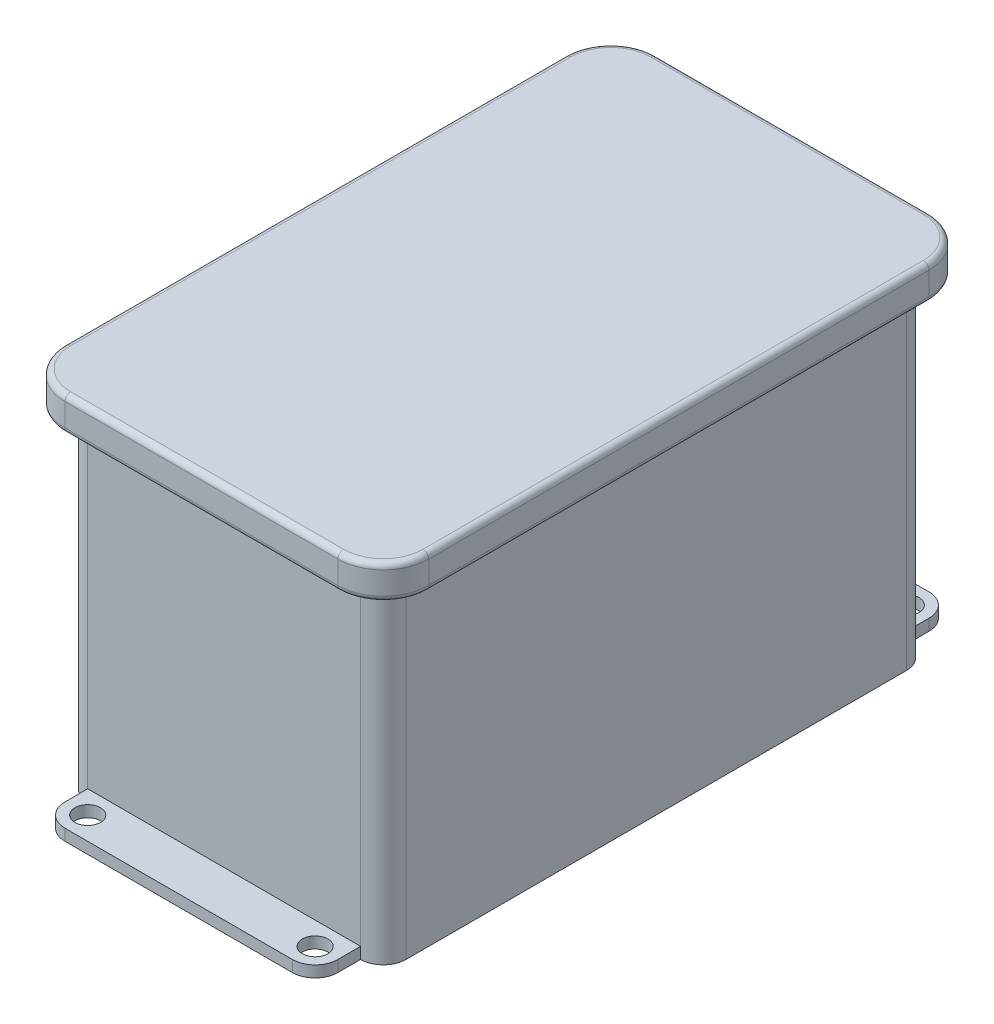
SolidWorks part; units mm, degrees
ref_plane "Front" through (0, 0, 0) normal (0, 0, 1) x (1, 0, 0)
ref_plane "Top" through (0, 0, 0) normal (0, 1, 0) x (1, 0, 0)
ref_plane "Right" through (0, 0, 0) normal (1, 0, 0) x (0, 0, -1)
sketch "Sketch1" plane through (0, 0, 0) normal (0, 1, 0) x (1, 0, 0)
  line L1 (0, 0) -> (88.9, 0)
  line L2 (0, 0) -> (0, 152.4)
  line L3 (0, 152.4) -> (88.9, 152.4)
  line L4 (88.9, 0) -> (88.9, 152.4)
  dimension "D1" = 152.4
  dimension "D2" = 88.9
extrude "Boss-Extrude1" add sketch "Sketch1" along normal blind 101.6
sketch "Sketch2" plane through (0, 0, 0) normal (0, -1, 0) x (1, 0, 0)
  line L0 (44.45, -152.4) -> (44.45, -158.75) construction
  line L1 (76.2, -158.75) -> (12.7, -158.75) construction
  line L2 (76.2, -165.1) -> (12.7, -165.1)
  line L4 (0, 0) -> (0, -152.4)
  line L5 (0, -152.4) -> (88.9, -152.4)
  line L6 (88.9, -152.4) -> (88.9, 0)
  line L7 (88.9, 0) -> (0, 0)
  line L9 (0, -152.4) -> (88.9, -152.4)
  line L12 (6.35, -158.75) -> (6.35, -152.4)
  line L14 (82.55, -158.75) -> (82.55, -152.4)
  arc A0 (76.2, -165.1) -> (82.55, -158.75) centre (76.2, -158.75) ccw
  arc A1 (6.35, -158.75) -> (12.7, -165.1) centre (12.7, -158.75) ccw
  circle A2 centre (12.7, -158.75) radius 3.5719
  circle A3 centre (76.2, -158.75) radius 3.5719
  point P8 (44.45, -158.75)
  point P12 (44.45, -158.75)
  dimension "D3" = 7.1437
  dimension "D2" = 76.2
  dimension "D4" = 12.7
  dimension "D5" = 6.35
  dimension "D1" = 0
extrude "Boss-Extrude2" add sketch "Sketch2" against normal blind 3.175 separate body contours L12 A1 L2 A0 L14 L9 A3 A2
ref_plane "Plane1" through (0, 0, -76.2) normal (0, 0, -1) x (-1, 0, 0)
mirror "Mirror2" about plane through (0, 0, -76.2) normal (0, 0, -1) of bodies 102
fillet "Fillet1" radius 6.35 4 edges at (88.9, 50.8, -152.4) (88.9, 50.8, 0) (0, 50.8, 0) (0, 50.8, -152.4)
sketch "Sketch4" plane through (0, 101.6, 0) normal (0, 1, 0) x (1, 0, 0)
  line L0 (95.25, 6.35) -> (95.25, 146.05)
  line L1 (82.55, 158.75) -> (6.35, 158.75)
  line L2 (-6.35, 146.05) -> (-6.35, 6.35)
  line L3 (6.35, -6.35) -> (82.55, -6.35)
  line L4 (88.9, 6.35) -> (88.9, 146.05)
  line L5 (82.55, 152.4) -> (6.35, 152.4)
  line L6 (0, 146.05) -> (0, 6.35)
  line L7 (6.35, 0) -> (82.55, 0)
  line L8 (88.9, 6.35) -> (88.9, 146.05) construction
  line L9 (82.55, 152.4) -> (6.35, 152.4) construction
  line L10 (0, 146.05) -> (0, 6.35) construction
  line L11 (6.35, 0) -> (82.55, 0) construction
  arc A0 (95.25, 146.05) -> (82.55, 158.75) centre (82.55, 146.05) ccw
  arc A1 (6.35, 158.75) -> (-6.35, 146.05) centre (6.35, 146.05) ccw
  arc A2 (-6.35, 6.35) -> (6.35, -6.35) centre (6.35, 6.35) ccw
  arc A3 (82.55, -6.35) -> (95.25, 6.35) centre (82.55, 6.35) ccw
  arc A4 (88.9, 146.05) -> (82.55, 152.4) centre (82.55, 146.05) ccw
  arc A5 (6.35, 152.4) -> (0, 146.05) centre (6.35, 146.05) ccw
  arc A6 (0, 6.35) -> (6.35, 0) centre (6.35, 6.35) ccw
  arc A7 (82.55, 0) -> (88.9, 6.35) centre (82.55, 6.35) ccw
  arc A8 (88.9, 146.05) -> (82.55, 152.4) centre (82.55, 146.05) ccw construction
  arc A9 (6.35, 152.4) -> (0, 146.05) centre (6.35, 146.05) ccw construction
  arc A10 (0, 6.35) -> (6.35, 0) centre (6.35, 6.35) ccw construction
  arc A11 (82.55, 0) -> (88.9, 6.35) centre (82.55, 6.35) ccw construction
  dimension "D1" = 0
  dimension "D2" = 6.35
extrude "Boss-Extrude3" add sketch "Sketch4" against normal blind 9.525
fillet "Fillet2" radius 1.5875 16 edges at (-2.6303, 92.075, -155.0303) (44.45, 92.075, -158.75) (91.5303, 92.075, -155.0303) (95.25, 92.075, -76.2) (91.5303, 92.075, 2.6303) (44.45, 92.075, 6.35) (-2.6303, 92.075, 2.6303) (44.45, 101.6, -158.75) (91.5303, 101.6, -155.0303) (95.25, 101.6, -76.2) (91.5303, 101.6, 2.6303) (44.45, 101.6, 6.35) (-2.6303, 101.6, 2.6303) (-6.35, 101.6, -76.2) (-6.35, 92.075, -76.2) (-2.6303, 101.6, -155.0303)
